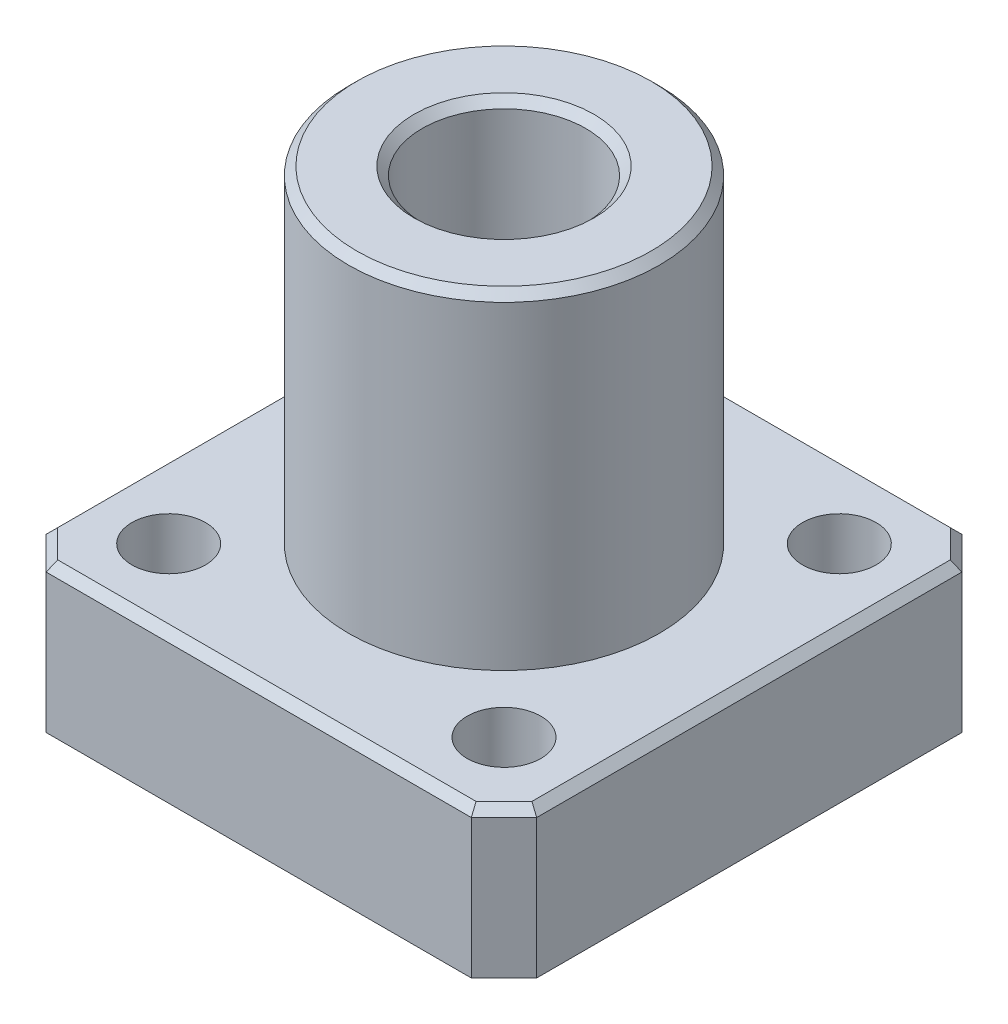
SolidWorks part; units mm, degrees
ref_plane "Face" through (0, 0, 0) normal (0, 0, 1) x (1, 0, 0)
ref_plane "Dessus" through (0, 0, 0) normal (0, 1, 0) x (1, 0, 0)
ref_plane "Droite" through (0, 0, 0) normal (1, 0, 0) x (0, 0, -1)
sketch "Esquisse1" plane through (0, 0, 0) normal (0, 1, 0) x (1, 0, 0)
  line L0 (0, 15) -> (30, 15) construction
  line L1 (0, 0) -> (30, 0)
  line L2 (0, 0) -> (0, 30)
  line L3 (0, 30) -> (30, 30)
  line L4 (30, 0) -> (30, 30)
  line L5 (15, 30) -> (15, 0) construction
  line L6 (0, 30) -> (30, 0) construction
  circle A0 centre (4.747, 25.253) radius 2.25
  circle A1 centre (25.253, 25.253) radius 2.25
  circle A2 centre (25.253, 4.747) radius 2.25
  circle A3 centre (4.747, 4.747) radius 2.25
  dimension "D2" = 4.5
  dimension "D1" = 30
  dimension "D3" = 29
extrude "Extrusion1" add sketch "Esquisse1" along normal blind 9
sketch "Esquisse2" plane through (0, 9, 0) normal (0, 1, 0) x (1, 0, 0)
  line L0 (0, 30) -> (30, 0) construction
  line L1 (0, 0) -> (30, 30) construction
  line L2 (30, 0) -> (30, 30) construction
  circle A0 centre (15, 15) radius 9.5
  dimension "D1" = 19
extrude "Extrusion2" add sketch "Esquisse2" along normal blind 20
chamfer "Chanfrein1" distance 2 angle 45 4 edges at (0, 4.5, -30) (30, 4.5, -30) (30, 4.5, 0) (0, 4.5, 0)
sketch "Esquisse3" plane through (0, 29, 0) normal (0, 1, 0) x (1, 0, 0)
  circle A0 centre (15, 15) radius 5
  dimension "D1" = 10
extrude "Extrusion3" cut sketch "Esquisse3" against normal up to next
chamfer "Chanfrein2" distance 0.5 angle 45 11 edges at (15, 0, -20) (29, 9, -29) (30, 9, -15) (29, 9, -1) (15, 9, 0) (1, 9, -1) (0, 9, -15) (1, 9, -29) (15, 9, -30) (15, 29, -5.5) (15, 29, -10)
